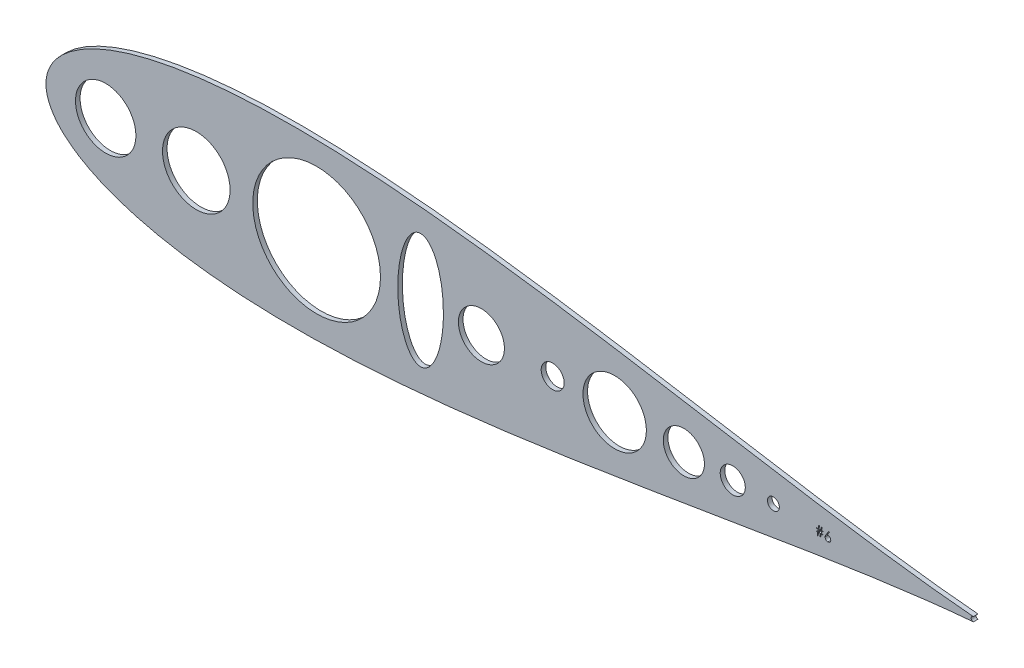
SolidWorks part; units mm, degrees
ref_plane "Front Plane" through (0, 0, 0) normal (0, 0, 1) x (1, 0, 0)
ref_plane "Top Plane" through (0, 0, 0) normal (0, 1, 0) x (1, 0, 0)
ref_plane "Right Plane" through (0, 0, 0) normal (1, 0, 0) x (0, 0, -1)
sketch "Model" plane through (0, 0, 0) normal (0, 0, 1) x (1, 0, 0)
  line L0 (727.8331, 509.2636) -> (726.4908, 507.211)
  line L1 (727.482, 509.5393) -> (727.8331, 509.2636)
  line L2 (725.9657, 507.2212) -> (727.482, 509.5393)
  line L3 (724.2907, 507.5855) -> (723.4135, 507.5855)
  line L4 (724.2907, 507.9111) -> (724.2907, 507.5855)
  line L5 (723.4624, 507.9111) -> (724.2907, 507.9111)
  line L6 (723.7066, 509.5393) -> (723.4624, 507.9111)
  line L7 (723.3138, 509.5393) -> (723.7066, 509.5393)
  line L8 (723.0696, 507.9111) -> (723.3138, 509.5393)
  line L9 (722.0295, 507.9111) -> (723.0696, 507.9111)
  line L10 (722.2738, 509.5393) -> (722.0295, 507.9111)
  line L11 (721.881, 509.5393) -> (722.2738, 509.5393)
  line L12 (721.6367, 507.9111) -> (721.881, 509.5393)
  line L13 (720.6435, 507.9111) -> (721.6367, 507.9111)
  line L14 (720.6435, 507.5855) -> (720.6435, 507.9111)
  line L15 (721.5879, 507.5855) -> (720.6435, 507.5855)
  line L16 (721.4118, 506.4132) -> (721.5879, 507.5855)
  line L17 (720.5133, 506.4132) -> (721.4118, 506.4132)
  line L18 (720.5133, 506.0876) -> (720.5133, 506.4132)
  line L19 (721.363, 506.0876) -> (720.5133, 506.0876)
  line L20 (721.0994, 504.3291) -> (721.363, 506.0876)
  line L21 (721.4933, 504.3291) -> (721.0994, 504.3291)
  line L22 (721.7568, 506.0876) -> (721.4933, 504.3291)
  line L23 (722.7958, 506.0876) -> (721.7568, 506.0876)
  line L24 (722.5322, 504.3291) -> (722.7958, 506.0876)
  line L25 (722.9261, 504.3291) -> (722.5322, 504.3291)
  line L26 (723.1896, 506.0876) -> (722.9261, 504.3291)
  line L27 (724.1605, 506.0876) -> (723.1896, 506.0876)
  line L28 (724.1605, 506.4132) -> (724.1605, 506.0876)
  line L29 (723.2385, 506.4132) -> (724.1605, 506.4132)
  line L30 (723.4135, 507.5855) -> (723.2385, 506.4132)
  line L31 (723.0207, 507.5855) -> (721.9807, 507.5855)
  line L32 (722.8447, 506.4132) -> (723.0207, 507.5855)
  line L33 (721.8057, 506.4132) -> (722.8447, 506.4132)
  line L34 (721.9807, 507.5855) -> (721.8057, 506.4132)
  arc A0 (807.168, 506.1079) -> (807.2931, 506.1246) centre (807.0631, 507.3687) ccw
  arc A1 (807.2963, 508.6123) -> (807.2931, 506.1246) centre (807.2947, 507.3684) ccw
  circle A2 centre (328.0596, 507.3687) radius 16.6848
  circle A3 centre (696.8327, 507.3687) radius 3.2907
  circle A4 centre (674.3907, 507.3687) radius 6.9292
  circle A5 centre (647.3866, 507.3687) radius 11.3532
  circle A6 centre (535.5664, 507.3687) radius 12.7
  circle A7 centre (378.0864, 507.3687) radius 18.669
  circle A8 centre (444.5488, 507.3687) radius 35.2696
  circle A9 centre (609.1648, 507.3687) radius 17.5111
  circle A10 centre (574.9364, 507.3687) radius 6.35
  arc A11 (807.2963, 508.6123) -> (807.168, 508.6296) centre (807.0631, 507.3687) ccw
  ellipse E0 centre (501.9977, 507.3687) end of major axis (501.9977, 539.226) minor radius 12.6216
  spline S0 degree 3 poles (807.168, 508.6296) (806.7556, 508.6639) (803.6475, 508.9257) (797.5266, 509.4915) (788.4411, 510.4366) (778.3677, 511.5964) (767.3443, 512.9777) (755.4224, 514.5821) (742.6536, 516.4059) (729.093, 518.4396) (714.7983, 520.6689) (699.8294, 523.0737) (684.2482, 525.6293) (668.1182, 528.3063) (651.5048, 531.0707) (634.4746, 533.8852) (617.0958, 536.7089) (599.4377, 539.4984) (581.5711, 542.2084) (563.5679, 544.7922) (545.5012, 547.2027) (527.4456, 549.3927) (509.4769, 551.3163) (491.6721, 552.9289) (474.1097, 554.1886) (456.8692, 555.0565) (440.0317, 555.4976) (423.6795, 555.4812) (407.8958, 554.9814) (392.7656, 553.9787) (378.3752, 552.4585) (364.8124, 550.4139) (352.1677, 547.8442) (340.5347, 544.758) (330.0117, 541.1735) (320.7037, 537.1225) (312.7237, 532.6587) (306.191, 527.8727) (301.2155, 522.9208) (297.8469, 518.0648) (295.9686, 513.6837) (295.2101, 510.1692) (295.0373, 507.3687) (295.2101, 504.5682) (295.9686, 501.0538) (297.8469, 496.6727) (301.2155, 491.8167) (306.191, 486.8648) (312.7237, 482.0788) (320.7037, 477.615) (330.0117, 473.564) (340.5347, 469.9794) (352.1677, 466.8933) (364.8124, 464.3236) (378.3752, 462.279) (392.7656, 460.7588) (407.8958, 459.756) (423.6795, 459.2563) (440.0317, 459.2399) (456.8692, 459.6809) (474.1097, 460.5488) (491.6721, 461.8086) (509.4769, 463.4212) (527.4456, 465.3448) (545.5012, 467.5348) (563.5679, 469.9453) (581.5711, 472.5291) (599.4377, 475.2391) (617.0958, 478.0286) (634.4746, 480.8523) (651.5048, 483.6668) (668.1182, 486.4312) (684.2482, 489.1081) (699.8294, 491.6638) (714.7983, 494.0686) (729.093, 496.2979) (742.6536, 498.3316) (755.4224, 500.1554) (767.3443, 501.7597) (778.3677, 503.1411) (788.4411, 504.3009) (797.5266, 505.246) (803.6475, 505.8118) (806.7556, 506.0736) (807.168, 506.1079) knots 0.020157 0.020157 0.020157 0.020157 0.021271 0.028553 0.036781 0.04592 0.055932 0.066773 0.078397 0.090755 0.103793 0.117456 0.131686 0.146422 0.1616 0.177156 0.193024 0.209135 0.225421 0.241812 0.258238 0.274629 0.290914 0.307025 0.322893 0.338448 0.353626 0.368361 0.38259 0.396253 0.40929 0.421647 0.43327 0.444109 0.454119 0.463255 0.471479 0.478755 0.485052 0.490344 0.49461 0.497833 0.5 0.502167 0.50539 0.509656 0.514948 0.521245 0.528521 0.536745 0.545881 0.555891 0.56673 0.578353 0.59071 0.603747 0.61741 0.631639 0.646374 0.661552 0.677107 0.692975 0.709086 0.725371 0.741762 0.758188 0.774579 0.790865 0.806976 0.822844 0.8384 0.853578 0.868314 0.882544 0.896207 0.909245 0.921603 0.933227 0.944068 0.95408 0.963219 0.971447 0.978729 0.979843 0.979843 0.979843 0.979843
  spline S1 degree 3 poles (726.4908, 507.211) (726.5802, 507.2253) (726.7545, 507.253) (726.9309, 507.2576) (727.0169, 507.2599) knots 0 0 0 0 0.512659 1 1 1 1
  spline S2 degree 3 poles (728.524, 505.7548) (728.522, 505.6837) (728.5179, 505.5438) (728.4774, 505.3401) (728.4145, 505.146) (728.3245, 504.9646) (728.2128, 504.7962) (728.0765, 504.647) (727.9206, 504.514) (727.7443, 504.4027) (727.5545, 504.3119) (727.3551, 504.2466) (727.1481, 504.2064) (727.0076, 504.2014) (726.9365, 504.1988) knots 0 0 0 0 0.085948 0.169125 0.250399 0.33229 0.413364 0.494172 0.576022 0.660757 0.745783 0.830044 0.914028 1 1 1 1
  spline S3 degree 3 poles (725.3979, 505.7456) (725.3996, 505.7979) (725.4031, 505.9048) (725.4276, 506.0665) (725.4668, 506.2321) (725.5108, 506.3725) (725.5573, 506.4876) (725.596, 506.5803) (725.6441, 506.6758) (725.6955, 506.7772) (725.7546, 506.8819) (725.819, 506.9918) (725.8902, 507.1051) (725.9402, 507.1819) (725.9657, 507.2212) knots 0 0 0 0 0.097818 0.199726 0.305276 0.415811 0.474472 0.537274 0.603657 0.674299 0.749834 0.828598 0.912378 1 1 1 1
  spline S4 degree 3 poles (726.9365, 504.1988) (726.8682, 504.2011) (726.7328, 504.2054) (726.5336, 504.2446) (726.3422, 504.308) (726.16, 504.3954) (725.9911, 504.5058) (725.8401, 504.6387) (725.7076, 504.7913) (725.5973, 504.9635) (725.5098, 505.1485) (725.4443, 505.3415) (725.4059, 505.5416) (725.4006, 505.6773) (725.3979, 505.7456) knots 0 0 0 0 0.084335 0.167052 0.249566 0.33274 0.415915 0.497828 0.580373 0.6646 0.749467 0.83251 0.915639 1 1 1 1
  spline S5 degree 3 poles (727.0169, 507.2599) (727.0686, 507.2585) (727.1702, 507.2557) (727.3194, 507.2347) (727.4628, 507.2016) (727.5998, 507.1533) (727.7308, 507.0916) (727.8566, 507.0177) (727.9749, 506.9277) (728.0872, 506.8271) (728.1891, 506.7158) (728.2794, 506.5976) (728.3552, 506.4728) (728.4167, 506.3414) (728.4644, 506.2035) (728.4992, 506.0595) (728.5198, 505.909) (728.5226, 505.8068) (728.524, 505.7548) knots 0 0 0 0 0.065231 0.128405 0.190067 0.250943 0.311546 0.372863 0.435024 0.499072 0.563091 0.62551 0.68668 0.747283 0.808563 0.870742 0.934341 1 1 1 1
  spline S6 degree 3 poles (725.8538, 505.7273) (725.8547, 505.693) (725.8565, 505.6257) (725.8727, 505.5265) (725.8974, 505.431) (725.9342, 505.3398) (725.978, 505.2514) (726.036, 505.1691) (726.1001, 505.0878) (726.1769, 505.0137) (726.2592, 504.9449) (726.3471, 504.8847) (726.4388, 504.8332) (726.5354, 504.7928) (726.6356, 504.7597) (726.7403, 504.7363) (726.8494, 504.7232) (726.9233, 504.721) (726.961, 504.7199) knots 0 0 0 0 0.061842 0.121262 0.180746 0.239231 0.298308 0.358183 0.420359 0.484792 0.549938 0.613718 0.676681 0.739154 0.8022 0.86674 0.93205 1 1 1 1
  spline S7 degree 3 poles (728.0681, 505.7273) (728.0673, 505.762) (728.0658, 505.8301) (728.0481, 505.9298) (728.0235, 506.026) (727.9863, 506.1183) (727.9381, 506.2061) (727.8793, 506.29) (727.8114, 506.3705) (727.7328, 506.4454) (727.6474, 506.5138) (727.5565, 506.5742) (727.4614, 506.6252) (727.3622, 506.6677) (727.2578, 506.6984) (727.1498, 506.7226) (727.0369, 506.7355) (726.9603, 506.7377) (726.9213, 506.7388) knots 0 0 0 0 0.061138 0.119994 0.178225 0.236256 0.294929 0.354716 0.41673 0.480664 0.545832 0.609758 0.672971 0.736017 0.799839 0.864775 0.931088 1 1 1 1
  spline S8 degree 3 poles (726.9213, 506.7388) (726.8826, 506.7377) (726.807, 506.7355) (726.6961, 506.7227) (726.5911, 506.6986) (726.4907, 506.6678) (726.3968, 506.6256) (726.3085, 506.5743) (726.2257, 506.5139) (726.1491, 506.4452) (726.0797, 506.3701) (726.02, 506.2896) (725.9684, 506.2056) (725.9265, 506.1176) (725.8938, 506.0255) (725.8702, 505.9298) (725.8571, 505.8298) (725.8549, 505.7619) (725.8538, 505.7273) knots 0 0 0 0 0.070599 0.137901 0.203196 0.26679 0.329106 0.390654 0.452653 0.515748 0.577926 0.63893 0.698351 0.757296 0.816394 0.876267 0.936817 1 1 1 1
  spline S9 degree 3 poles (726.961, 504.7199) (726.9987, 504.721) (727.0726, 504.7232) (727.1817, 504.7363) (727.2863, 504.7597) (727.3865, 504.7928) (727.4831, 504.8332) (727.5747, 504.8843) (727.6618, 504.9452) (727.7442, 505.0136) (727.8206, 505.0882) (727.8863, 505.1684) (727.9424, 505.2521) (727.9881, 505.3395) (728.0244, 505.4311) (728.0493, 505.5265) (728.0654, 505.6257) (728.0672, 505.693) (728.0681, 505.7273) knots 0 0 0 0 0.067962 0.133283 0.197835 0.260892 0.323377 0.38635 0.449638 0.514795 0.57924 0.641814 0.701359 0.760727 0.819222 0.878716 0.938147 1 1 1 1
sketch "Sketch2" plane through (0, 0, 0) normal (0, 0, 1) x (1, 0, 0)
  line L0 (727.8331, 509.2636) -> (726.4908, 507.211)
  line L1 (727.482, 509.5393) -> (727.8331, 509.2636)
  line L2 (725.9657, 507.2212) -> (727.482, 509.5393)
  line L3 (724.2907, 507.5855) -> (723.4135, 507.5855)
  line L4 (724.2907, 507.9111) -> (724.2907, 507.5855)
  line L5 (723.4624, 507.9111) -> (724.2907, 507.9111)
  line L6 (723.7066, 509.5393) -> (723.4624, 507.9111)
  line L7 (723.3138, 509.5393) -> (723.7066, 509.5393)
  line L8 (723.0696, 507.9111) -> (723.3138, 509.5393)
  line L9 (722.0295, 507.9111) -> (723.0696, 507.9111)
  line L10 (722.2738, 509.5393) -> (722.0295, 507.9111)
  line L11 (721.881, 509.5393) -> (722.2738, 509.5393)
  line L12 (721.6367, 507.9111) -> (721.881, 509.5393)
  line L13 (720.6435, 507.9111) -> (721.6367, 507.9111)
  line L14 (720.6435, 507.5855) -> (720.6435, 507.9111)
  line L15 (721.5879, 507.5855) -> (720.6435, 507.5855)
  line L16 (721.4118, 506.4132) -> (721.5879, 507.5855)
  line L17 (720.5133, 506.4132) -> (721.4118, 506.4132)
  line L18 (720.5133, 506.0876) -> (720.5133, 506.4132)
  line L19 (721.363, 506.0876) -> (720.5133, 506.0876)
  line L20 (721.0994, 504.3291) -> (721.363, 506.0876)
  line L21 (721.4933, 504.3291) -> (721.0994, 504.3291)
  line L22 (721.7568, 506.0876) -> (721.4933, 504.3291)
  line L23 (722.7958, 506.0876) -> (721.7568, 506.0876)
  line L24 (722.5322, 504.3291) -> (722.7958, 506.0876)
  line L25 (722.9261, 504.3291) -> (722.5322, 504.3291)
  line L26 (723.1896, 506.0876) -> (722.9261, 504.3291)
  line L27 (724.1605, 506.0876) -> (723.1896, 506.0876)
  line L28 (724.1605, 506.4132) -> (724.1605, 506.0876)
  line L29 (723.2385, 506.4132) -> (724.1605, 506.4132)
  line L30 (723.4135, 507.5855) -> (723.2385, 506.4132)
  line L31 (723.0207, 507.5855) -> (721.9807, 507.5855)
  line L32 (722.8447, 506.4132) -> (723.0207, 507.5855)
  line L33 (721.8057, 506.4132) -> (722.8447, 506.4132)
  line L34 (721.9807, 507.5855) -> (721.8057, 506.4132)
  arc A0 (807.168, 506.1079) -> (807.2931, 506.1246) centre (807.0631, 507.3687) ccw
  arc A1 (807.2963, 508.6123) -> (807.2931, 506.1246) centre (807.2947, 507.3684) ccw
  circle A2 centre (328.0596, 507.3687) radius 16.6848
  circle A3 centre (696.8327, 507.3687) radius 3.2907
  circle A4 centre (674.3907, 507.3687) radius 6.9292
  circle A5 centre (647.3866, 507.3687) radius 11.3532
  circle A6 centre (535.5664, 507.3687) radius 12.7
  circle A7 centre (378.0864, 507.3687) radius 18.669
  circle A8 centre (444.5488, 507.3687) radius 35.2696
  circle A9 centre (609.1648, 507.3687) radius 17.5111
  circle A10 centre (574.9364, 507.3687) radius 6.35
  arc A11 (807.2963, 508.6123) -> (807.168, 508.6296) centre (807.0631, 507.3687) ccw
  ellipse E0 centre (501.9977, 507.3687) end of major axis (501.9977, 539.226) minor radius 12.6216
  spline S0 degree 3 poles (807.168, 508.6296) (806.7556, 508.6639) (803.6475, 508.9257) (797.5266, 509.4915) (788.4411, 510.4366) (778.3677, 511.5964) (767.3443, 512.9777) (755.4224, 514.5821) (742.6536, 516.4059) (729.093, 518.4396) (714.7983, 520.6689) (699.8294, 523.0737) (684.2482, 525.6293) (668.1182, 528.3063) (651.5048, 531.0707) (634.4746, 533.8852) (617.0958, 536.7089) (599.4377, 539.4984) (581.5711, 542.2084) (563.5679, 544.7922) (545.5012, 547.2027) (527.4456, 549.3927) (509.4769, 551.3163) (491.6721, 552.9289) (474.1097, 554.1886) (456.8692, 555.0565) (440.0317, 555.4976) (423.6795, 555.4812) (407.8958, 554.9814) (392.7656, 553.9787) (378.3752, 552.4585) (364.8124, 550.4139) (352.1677, 547.8442) (340.5347, 544.758) (330.0117, 541.1735) (320.7037, 537.1225) (312.7237, 532.6587) (306.191, 527.8727) (301.2155, 522.9208) (297.8469, 518.0648) (295.9686, 513.6837) (295.2101, 510.1692) (295.0373, 507.3687) (295.2101, 504.5682) (295.9686, 501.0538) (297.8469, 496.6727) (301.2155, 491.8167) (306.191, 486.8648) (312.7237, 482.0788) (320.7037, 477.615) (330.0117, 473.564) (340.5347, 469.9794) (352.1677, 466.8933) (364.8124, 464.3236) (378.3752, 462.279) (392.7656, 460.7588) (407.8958, 459.756) (423.6795, 459.2563) (440.0317, 459.2399) (456.8692, 459.6809) (474.1097, 460.5488) (491.6721, 461.8086) (509.4769, 463.4212) (527.4456, 465.3448) (545.5012, 467.5348) (563.5679, 469.9453) (581.5711, 472.5291) (599.4377, 475.2391) (617.0958, 478.0286) (634.4746, 480.8523) (651.5048, 483.6668) (668.1182, 486.4312) (684.2482, 489.1081) (699.8294, 491.6638) (714.7983, 494.0686) (729.093, 496.2979) (742.6536, 498.3316) (755.4224, 500.1554) (767.3443, 501.7597) (778.3677, 503.1411) (788.4411, 504.3009) (797.5266, 505.246) (803.6475, 505.8118) (806.7556, 506.0736) (807.168, 506.1079) knots 0.020157 0.020157 0.020157 0.020157 0.021271 0.028553 0.036781 0.04592 0.055932 0.066773 0.078397 0.090755 0.103793 0.117456 0.131686 0.146422 0.1616 0.177156 0.193024 0.209135 0.225421 0.241812 0.258238 0.274629 0.290914 0.307025 0.322893 0.338448 0.353626 0.368361 0.38259 0.396253 0.40929 0.421647 0.43327 0.444109 0.454119 0.463255 0.471479 0.478755 0.485052 0.490344 0.49461 0.497833 0.5 0.502167 0.50539 0.509656 0.514948 0.521245 0.528521 0.536745 0.545881 0.555891 0.56673 0.578353 0.59071 0.603747 0.61741 0.631639 0.646374 0.661552 0.677107 0.692975 0.709086 0.725371 0.741762 0.758188 0.774579 0.790865 0.806976 0.822844 0.8384 0.853578 0.868314 0.882544 0.896207 0.909245 0.921603 0.933227 0.944068 0.95408 0.963219 0.971447 0.978729 0.979843 0.979843 0.979843 0.979843
  spline S1 degree 3 poles (726.4908, 507.211) (726.5802, 507.2253) (726.7545, 507.253) (726.9309, 507.2576) (727.0169, 507.2599) knots 0 0 0 0 0.512659 1 1 1 1
  spline S2 degree 3 poles (728.524, 505.7548) (728.522, 505.6837) (728.5179, 505.5438) (728.4774, 505.3401) (728.4145, 505.146) (728.3245, 504.9646) (728.2128, 504.7962) (728.0765, 504.647) (727.9206, 504.514) (727.7443, 504.4027) (727.5545, 504.3119) (727.3551, 504.2466) (727.1481, 504.2064) (727.0076, 504.2014) (726.9365, 504.1988) knots 0 0 0 0 0.085948 0.169125 0.250399 0.33229 0.413364 0.494172 0.576022 0.660757 0.745783 0.830044 0.914028 1 1 1 1
  spline S3 degree 3 poles (725.3979, 505.7456) (725.3996, 505.7979) (725.4031, 505.9048) (725.4276, 506.0665) (725.4668, 506.2321) (725.5108, 506.3725) (725.5573, 506.4876) (725.596, 506.5803) (725.6441, 506.6758) (725.6955, 506.7772) (725.7546, 506.8819) (725.819, 506.9918) (725.8902, 507.1051) (725.9402, 507.1819) (725.9657, 507.2212) knots 0 0 0 0 0.097818 0.199726 0.305276 0.415811 0.474472 0.537274 0.603657 0.674299 0.749834 0.828598 0.912378 1 1 1 1
  spline S4 degree 3 poles (726.9365, 504.1988) (726.8682, 504.2011) (726.7328, 504.2054) (726.5336, 504.2446) (726.3422, 504.308) (726.16, 504.3954) (725.9911, 504.5058) (725.8401, 504.6387) (725.7076, 504.7913) (725.5973, 504.9635) (725.5098, 505.1485) (725.4443, 505.3415) (725.4059, 505.5416) (725.4006, 505.6773) (725.3979, 505.7456) knots 0 0 0 0 0.084335 0.167052 0.249566 0.33274 0.415915 0.497828 0.580373 0.6646 0.749467 0.83251 0.915639 1 1 1 1
  spline S5 degree 3 poles (727.0169, 507.2599) (727.0686, 507.2585) (727.1702, 507.2557) (727.3194, 507.2347) (727.4628, 507.2016) (727.5998, 507.1533) (727.7308, 507.0916) (727.8566, 507.0177) (727.9749, 506.9277) (728.0872, 506.8271) (728.1891, 506.7158) (728.2794, 506.5976) (728.3552, 506.4728) (728.4167, 506.3414) (728.4644, 506.2035) (728.4992, 506.0595) (728.5198, 505.909) (728.5226, 505.8068) (728.524, 505.7548) knots 0 0 0 0 0.065231 0.128405 0.190067 0.250943 0.311546 0.372863 0.435024 0.499072 0.563091 0.62551 0.68668 0.747283 0.808563 0.870742 0.934341 1 1 1 1
  spline S6 degree 3 poles (725.8538, 505.7273) (725.8547, 505.693) (725.8565, 505.6257) (725.8727, 505.5265) (725.8974, 505.431) (725.9342, 505.3398) (725.978, 505.2514) (726.036, 505.1691) (726.1001, 505.0878) (726.1769, 505.0137) (726.2592, 504.9449) (726.3471, 504.8847) (726.4388, 504.8332) (726.5354, 504.7928) (726.6356, 504.7597) (726.7403, 504.7363) (726.8494, 504.7232) (726.9233, 504.721) (726.961, 504.7199) knots 0 0 0 0 0.061842 0.121262 0.180746 0.239231 0.298308 0.358183 0.420359 0.484792 0.549938 0.613718 0.676681 0.739154 0.8022 0.86674 0.93205 1 1 1 1
  spline S7 degree 3 poles (728.0681, 505.7273) (728.0673, 505.762) (728.0658, 505.8301) (728.0481, 505.9298) (728.0235, 506.026) (727.9863, 506.1183) (727.9381, 506.2061) (727.8793, 506.29) (727.8114, 506.3705) (727.7328, 506.4454) (727.6474, 506.5138) (727.5565, 506.5742) (727.4614, 506.6252) (727.3622, 506.6677) (727.2578, 506.6984) (727.1498, 506.7226) (727.0369, 506.7355) (726.9603, 506.7377) (726.9213, 506.7388) knots 0 0 0 0 0.061138 0.119994 0.178225 0.236256 0.294929 0.354716 0.41673 0.480664 0.545832 0.609758 0.672971 0.736017 0.799839 0.864775 0.931088 1 1 1 1
  spline S8 degree 3 poles (726.9213, 506.7388) (726.8826, 506.7377) (726.807, 506.7355) (726.6961, 506.7227) (726.5911, 506.6986) (726.4907, 506.6678) (726.3968, 506.6256) (726.3085, 506.5743) (726.2257, 506.5139) (726.1491, 506.4452) (726.0797, 506.3701) (726.02, 506.2896) (725.9684, 506.2056) (725.9265, 506.1176) (725.8938, 506.0255) (725.8702, 505.9298) (725.8571, 505.8298) (725.8549, 505.7619) (725.8538, 505.7273) knots 0 0 0 0 0.070599 0.137901 0.203196 0.26679 0.329106 0.390654 0.452653 0.515748 0.577926 0.63893 0.698351 0.757296 0.816394 0.876267 0.936817 1 1 1 1
  spline S9 degree 3 poles (726.961, 504.7199) (726.9987, 504.721) (727.0726, 504.7232) (727.1817, 504.7363) (727.2863, 504.7597) (727.3865, 504.7928) (727.4831, 504.8332) (727.5747, 504.8843) (727.6618, 504.9452) (727.7442, 505.0136) (727.8206, 505.0882) (727.8863, 505.1684) (727.9424, 505.2521) (727.9881, 505.3395) (728.0244, 505.4311) (728.0493, 505.5265) (728.0654, 505.6257) (728.0672, 505.693) (728.0681, 505.7273) knots 0 0 0 0 0.067962 0.133283 0.197835 0.260892 0.323377 0.38635 0.449638 0.514795 0.57924 0.641814 0.701359 0.760727 0.819222 0.878716 0.938147 1 1 1 1
extrude "Boss-Extrude1" add sketch "Sketch2" along normal blind 2.54 contours A11 S0 A0 A1 L3 L30 L29 L28 L27 L26 L25 L24 L23 L22 L21 L20 L19 L18 L17 L16 L15 L14 L13 L12 L11 L10 L9 L8 L7 L6 L5 L4 A2 A3 A4 A5 A6 A7 A8 A9 A10
